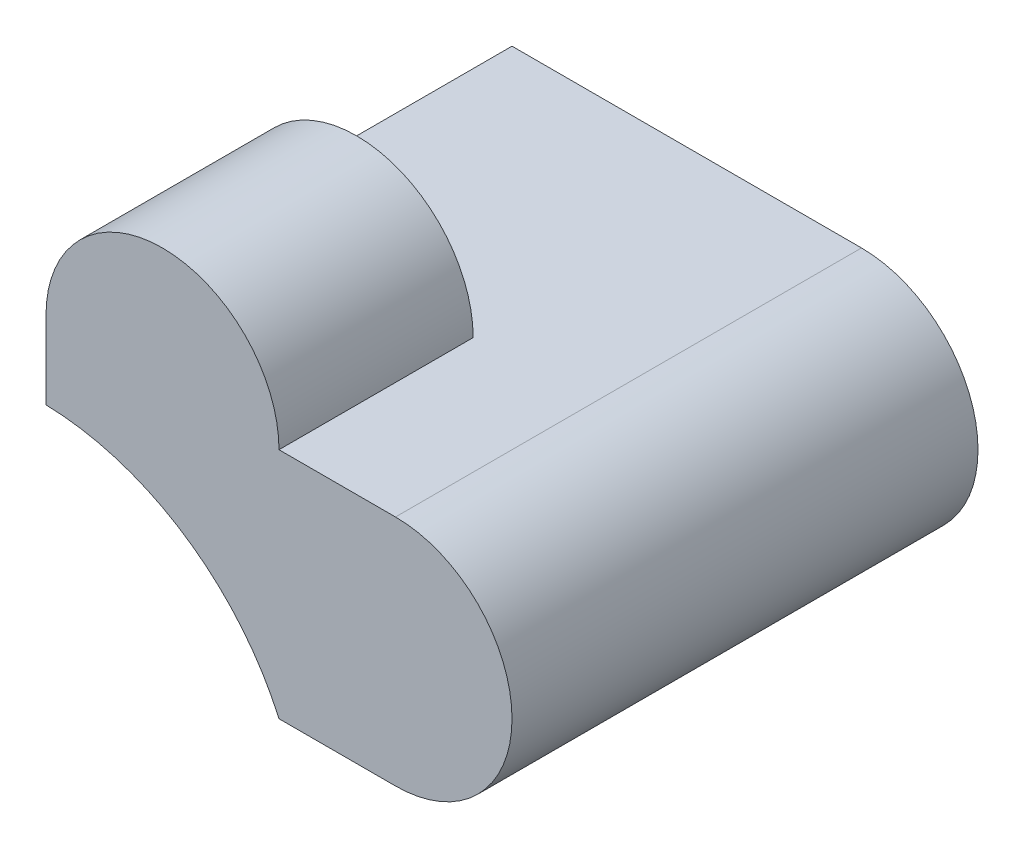
SolidWorks part; units mm, degrees
ref_plane "Front" through (0, 0, 0) normal (0, 0, 1) x (1, 0, 0)
ref_plane "Top" through (0, 0, 0) normal (0, 1, 0) x (1, 0, 0)
ref_plane "Right" through (0, 0, 0) normal (1, 0, 0) x (0, 0, -1)
sketch "Sketch1" plane through (0, 0, 0) normal (0, 1, 0) x (1, 0, 0)
  line L1 (-3, -3) -> (3, -3)
  line L2 (-3, -3) -> (-3, 3)
  line L3 (-3, 3) -> (3, 3)
  line L4 (3, -3) -> (3, 3)
  line L5 (-3, -3) -> (3, 3) construction
  line L6 (-3, 3) -> (3, -3) construction
  point P0 (0, 0)
  dimension "D1" = 6
  dimension "D2" = 6
extrude "Boss-Extrude1" add sketch "Sketch1" along normal blind 5
sketch "Sketch2" plane through (0, 0, 3) normal (0, 0, 1) x (1, 0, 0)
  line L0 (-3, 5) -> (-3, 0) construction
  line L1 (-3, 0) -> (3, 0) construction
  line L2 (0, 3) -> (1.5, 3)
  line L6 (-3, 0) -> (3, 0)
  line L7 (3, 0) -> (3, 5)
  line L8 (3, 5) -> (-3, 5)
  line L9 (-3, 5) -> (-3, 0)
  line L10 (-3, 0) -> (3, 0)
  line L11 (3, 0) -> (3, 5)
  line L12 (3, 5) -> (-3, 5)
  line L13 (-3, 5) -> (-3, 0)
  arc A0 (-3, 3) -> (0, 3) centre (-1.5, 3) cw
  arc A1 (1.5, 0) -> (1.5, 3) centre (1.5, 1.5) ccw
  line M7 (3, 0) -> (3, 5)
  line M8 (3, 5) -> (-3, 5)
  line M9 (-3, 5) -> (-3, 0)
  dimension "D3" = 1.5
  dimension "D6" = 1.5
  dimension "D7" = 1.5
  dimension "D1" = 3
  dimension "D2" = 3
  dimension "D4" = 3
  dimension "D8" = 1.5
  dimension "D5" = 0
extrude "Cut-Extrude1" cut sketch "Sketch2" against normal blind 10 contours A1 L11 A0 L2 M8 M9 | A1 L10 M7
sketch "Sketch3" plane through (0, 0, 3) normal (0, 0, 1) x (1, 0, 0)
  line L0 (-3, 3) -> (-3, 0) construction
  line L1 (-3, 0) -> (1.5, 0) construction
  line L5 (-3, 0) -> (1.5, 0)
  line L6 (1.5, 3) -> (0, 3)
  line L7 (-3, 3) -> (-3, 0)
  line L8 (-3, 0) -> (1.5, 0)
  line L9 (1.5, 3) -> (0, 3)
  line L10 (-3, 3) -> (-3, 0)
  arc A0 (-3, 2) -> (0, 0) centre (-3.0819, -1.3729) cw
  arc A3 (1.5, 0) -> (1.5, 3) centre (1.5, 1.5) ccw
  arc A4 (0, 3) -> (-3, 3) centre (-1.5, 3) ccw
  arc A5 (1.5, 0) -> (1.5, 3) centre (1.5, 1.5) ccw
  arc A6 (0, 3) -> (-3, 3) centre (-1.5, 3) ccw
  line M2 (-3, 0) -> (1.5, 0)
  dimension "D3" = 0
  dimension "D1" = 2
  dimension "D2" = 0
extrude "Cut-Extrude2" cut sketch "Sketch3" against normal blind 2.5 and the other way through all contours A0 L10 M2
sketch "Sketch4" plane through (-3, 0, 0) normal (-1, 0, 0) x (0, 0, 1)
  line L0 (-3, 3) -> (3, 3) construction
  line L1 (0.5, 3) -> (-3, 3)
  line L2 (0.5, 3) -> (0.5, 4.5)
  line L3 (0.5, 4.5) -> (-3, 4.5)
  line L4 (-3, 3) -> (-3, 4.5)
extrude "Cut-Extrude3" cut sketch "Sketch4" against normal blind 12.5
